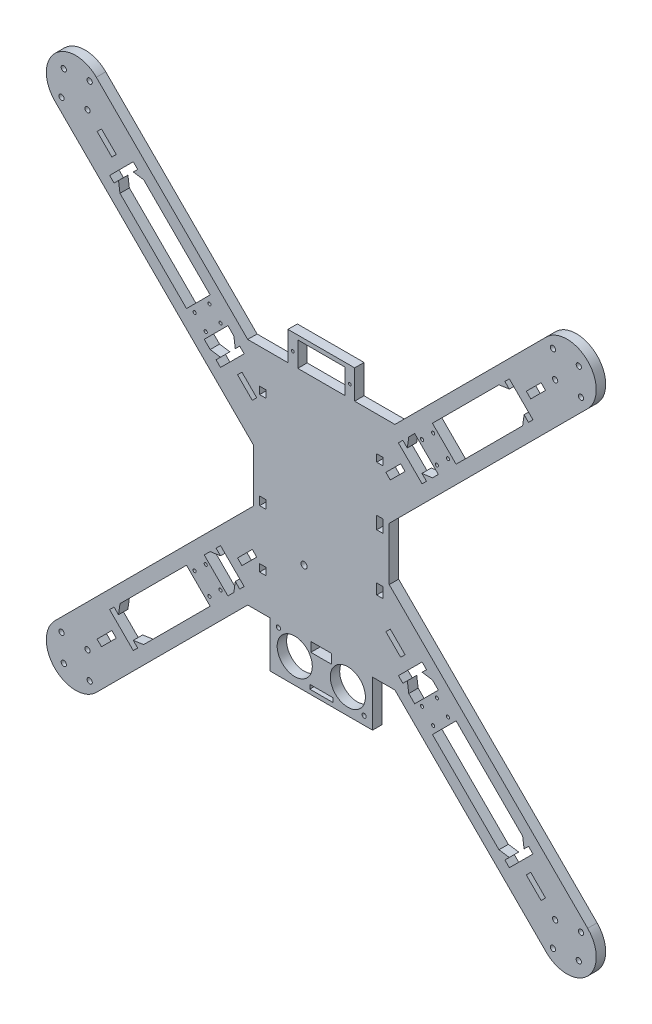
SolidWorks part; units mm, degrees
material "Custom Plastic"
ref_plane "Front Plane" through (0, 0, 0) normal (0, 0, 1) x (1, 0, 0)
ref_plane "Top Plane" through (0, 0, 0) normal (0, 1, 0) x (1, 0, 0)
ref_plane "Right Plane" through (0, 0, 0) normal (1, 0, 0) x (0, 0, -1)
sketch "Sketch1" plane through (0, 0, 0) normal (0, 0, 1) x (1, 0, 0)
  line L0 (117.5, 117.5) -> (-117.5, 117.5) construction
  line L1 (-117.5, 117.5) -> (117.5, -117.5) construction
  line L2 (117.5, -117.5) -> (-117.5, -117.5) construction
  line L3 (-117.5, -117.5) -> (117.5, 117.5) construction
  line L4 (117.5, 117.5) -> (117.5, -117.5) construction
  line L5 (-117.5, 117.5) -> (-117.5, -117.5) construction
  line L6 (0, 117.5) -> (0, -117.5) construction
  line L7 (35.201, 55) -> (15.95, 55)
  line L8 (-32.5, 55) -> (32.5, 55) construction
  line L9 (-35.201, 55) -> (-107.6005, 127.3995)
  line L10 (-127.3995, 107.6005) -> (-32.5, 12.701)
  line L11 (-117.5, 0) -> (117.5, 0) construction
  line L12 (-32.5, 12.701) -> (-32.5, -12.701)
  line L13 (32.5, 55) -> (32.5, -55) construction
  line L14 (32.5, -55) -> (-32.5, -55) construction
  line L15 (-32.5, -55) -> (-32.5, 55) construction
  line L16 (32.5, 55) -> (-32.5, -55) construction
  line L17 (-24.5, -55) -> (-24.5, -77)
  line L18 (-127.3995, -107.6005) -> (-32.5, -12.701)
  line L19 (-24.5, -77) -> (24.5, -77)
  line L20 (-35.201, -55) -> (-107.6005, -127.3995)
  line L21 (35.201, -55) -> (24.5, -55)
  line L22 (35.201, -55) -> (107.6005, -127.3995)
  line L23 (127.3995, -107.6005) -> (32.5, -12.701)
  line L24 (32.5, 12.701) -> (32.5, -12.701)
  line L25 (127.3995, 107.6005) -> (32.5, 12.701)
  line L26 (35.201, 55) -> (107.6005, 127.3995)
  line L27 (24.5, -55) -> (24.5, -77)
  line L28 (-24.5, -55) -> (-35.201, -55)
  line L29 (-15.95, 55) -> (-15.95, 68.8)
  line L30 (-15.95, 68.8) -> (15.95, 68.8)
  line L31 (15.95, 55) -> (15.95, 68.8)
  line L32 (-15.95, 55) -> (-35.201, 55)
  arc A0 (-107.6005, 127.3995) -> (-127.3995, 107.6005) centre (-117.5, 117.5) ccw
  arc A12 (-107.6005, -127.3995) -> (-127.3995, -107.6005) centre (-117.5, -117.5) cw
  arc A16 (107.6005, -127.3995) -> (127.3995, -107.6005) centre (117.5, -117.5) ccw
  arc A24 (107.6005, 127.3995) -> (127.3995, 107.6005) centre (117.5, 117.5) cw
  point P3 (0, 0)
  point P18 (0, 0)
  point P21 (0, -77)
  point P26 (0, 68.8)
  point P33 (-117.5, 117.5)
  point P34 (-32.5, 0)
  point P65 (0, -55)
  point P80 (0, 55)
  dimension "D3" = 14
  dimension "D8" = 24.5
  dimension "D7" = 22
  dimension "D1" = 235
  dimension "D2" = 235
  dimension "D4" = 65
  dimension "D5" = 110
  dimension "D6" = 28
  dimension "D9" = 13.8
  dimension "D10" = 31.9
extrude "Boss-Extrude1" add sketch "Sketch1" against normal blind 4.5
sketch "Sketch4" plane through (0, 0, 0) normal (0, 0, 1) x (1, 0, 0)
  line L0 (0, 0) -> (0, 55) construction
  line L2 (0, 0) -> (-32.5, 0) construction
  line L3 (-32.5, 12.701) -> (-32.5, -12.701) construction
  line L4 (-32.5, 0) -> (-32.5, 12.701) construction
  line L5 (-32.5, 12.701) -> (-127.3995, 107.6005) construction
  line L6 (-35.201, 55) -> (-107.6005, 127.3995) construction
  line L7 (-107.6005, 127.3995) -> (-127.3995, 107.6005) construction
  line L8 (-110.7825, 124.2175) -> (-124.2175, 110.7825) construction
  line L9 (-123.1569, 123.1569) -> (-111.8431, 111.8431) construction
  circle A20 centre (-110.7825, 124.2175) radius 1.25
  circle A21 centre (-124.2175, 110.7825) radius 1.25
  circle A22 centre (-123.1569, 123.1569) radius 1.25
  circle A23 centre (-111.8431, 111.8431) radius 1.25
  circle A24 centre (111.8431, 111.8431) radius 1.25
  circle A25 centre (110.7825, 124.2175) radius 1.25
  circle A26 centre (123.1569, 123.1569) radius 1.25
  circle A27 centre (124.2175, 110.7825) radius 1.25
  circle A28 centre (111.8431, -111.8431) radius 1.25
  circle A29 centre (124.2175, -110.7825) radius 1.25
  circle A30 centre (123.1569, -123.1569) radius 1.25
  circle A31 centre (110.7825, -124.2175) radius 1.25
  circle A32 centre (-111.8431, -111.8431) radius 1.25
  circle A33 centre (-110.7825, -124.2175) radius 1.25
  circle A34 centre (-123.1569, -123.1569) radius 1.25
  circle A35 centre (-124.2175, -110.7825) radius 1.25
  point P16 (-117.5, 117.5)
  point P19 (-117.5, 117.5)
  point P26 (-117.5, 117.5)
  point P62 (0, 0)
  dimension "D1" = 55
  dimension "D4" = 2.5
  dimension "D2" = 19
  dimension "D5" = 35.201
  dimension "D3" = 16
extrude "Cut-Extrude1" cut sketch "Sketch4" against normal blind 4.5
sketch "Sketch5" plane through (0, 0, 0) normal (0, 0, 1) x (1, 0, 0)
  line L4 (0, 0) -> (0, 14.0392) construction
  line L6 (15.95, 68.8) -> (-15.95, 68.8) construction
  line L7 (-11.25, 66.8) -> (-11.25, 55)
  line L8 (-11.25, 55) -> (11.25, 55)
  line L9 (11.25, 55) -> (11.25, 66.8)
  line L10 (11.25, 66.8) -> (-11.25, 66.8)
  line L12 (0, 66.8) -> (0, 55) construction
  line L13 (-13.65, 60.9) -> (13.65, 60.9) construction
  circle A2 centre (-13.65, 60.9) radius 0.65
  circle A3 centre (13.65, 60.9) radius 0.65
  point P20 (0, 60.9)
  point P21 (0, 60.9)
  dimension "D8" = 1.3
  dimension "D9" = 1.3
  dimension "D2" = 2
  dimension "D10" = 27.3
  dimension "D11" = 22.5
  dimension "D12" = 11.8
extrude "Cut-Extrude2" cut sketch "Sketch5" against normal blind 4.5
sketch "Sketch6" plane through (0, 0, 0) normal (0, 0, 1) x (1, 0, 0)
  line L1 (-11.25, 55) -> (11.25, 55) construction
  circle A0 centre (-8.25, -25) radius 1.5
  dimension "D3" = 3
  dimension "D1" = 80
  dimension "D2" = 3
extrude "Cut-Extrude3" cut sketch "Sketch6" against normal blind 4.5
sketch "Sketch7" plane through (0, 0, 0) normal (0, 0, 1) x (1, 0, 0)
  line L0 (-22.5, -55) -> (-22.5, -75) construction
  line L5 (-22.5, -75) -> (22.5, -75) construction
  line L6 (22.5, -75) -> (22.5, -55) construction
  line L7 (22.5, -55) -> (-22.5, -55) construction
  line L8 (0, -55) -> (0, -75) construction
  line L9 (-12.7, -65) -> (0, -65) construction
  line L10 (-24.5, -77) -> (24.5, -77) construction
  line L11 (-24.5, -55) -> (-24.5, -77) construction
  line L12 (-5, -55) -> (-5, -59.5)
  line L13 (-5, -59.5) -> (5, -59.5)
  line L15 (5, -55) -> (-5, -55)
  line L16 (-5.5, -75) -> (-5.5, -73)
  line L17 (-5.5, -73) -> (5.5, -73)
  line L21 (5.5, -75) -> (-5.5, -75)
  line L22 (5, -55) -> (5, -59.5)
  line L23 (5.5, -75) -> (5.5, -73)
  circle A5 centre (-20.5, -57) radius 1
  circle A6 centre (-12.7, -65) radius 8.4
  circle A7 centre (12.7, -65) radius 8.4
  circle A8 centre (20.5, -73) radius 1
  point P25 (0, -59.5)
  point P26 (0, -73)
  dimension "D3" = 2
  dimension "D6" = 20
  dimension "D13" = 5.5
  dimension "D5" = 45
  dimension "D1" = 2
  dimension "D4" = 16.8
  dimension "D14" = 2
  dimension "D2" = 2
  dimension "D7" = 2
  dimension "D8" = 2
  dimension "D9" = 12.7
  dimension "D10" = 5
  dimension "D11" = 4.5
  dimension "D12" = 2
  dimension "D15" = 2
  dimension "D16" = 2
extrude "Cut-Extrude4" cut sketch "Sketch7" against normal blind 4.5
sketch "Sketch8" plane through (0, 0, 0) normal (0, 0, 1) x (1, 0, 0)
  line L0 (101.2365, -89.9228) -> (89.9228, -101.2365)
  line L1 (89.9228, -101.2365) -> (87.8015, -99.1152)
  line L2 (36.8898, -48.2035) -> (48.2035, -36.8898)
  line L3 (48.2035, -36.8898) -> (50.3249, -39.0111)
  line L4 (105.4792, -85.6802) -> (85.6802, -105.4792) construction
  line L5 (127.3995, -107.6005) -> (32.5, -12.701) construction
  line L6 (35.201, -55) -> (107.6005, -127.3995) construction
  line L7 (40.0718, -37.9505) -> (37.9505, -40.0718)
  line L8 (115.8431, -107.8431) -> (111.8431, -111.8431) construction
  line L9 (37.9505, -40.0718) -> (30.8794, -33.0007)
  line L10 (50.3249, 39.0111) -> (48.2035, 36.8898)
  line L11 (30.8794, -33.0007) -> (33.0007, -30.8794)
  line L12 (33.0007, -30.8794) -> (40.0718, -37.9505)
  line L13 (42.5467, -42.5467) -> (39.0111, -39.0111) construction
  line L14 (35.201, -55) -> (107.6005, -127.3995) construction
  line L15 (100.1759, -98.0546) -> (98.0546, -100.1759)
  line L16 (98.0546, -100.1759) -> (105.1256, -107.247)
  line L17 (105.1256, -107.247) -> (107.247, -105.1256)
  line L18 (107.247, -105.1256) -> (100.1759, -98.0546)
  line L19 (99.1152, -99.1152) -> (95.5797, -95.5797) construction
  line L20 (-101.2365, -89.9228) -> (-99.1152, -87.8015)
  line L21 (-100.1759, -98.0546) -> (-107.247, -105.1256)
  line L22 (-107.247, -105.1256) -> (-105.1256, -107.247)
  line L23 (-105.1256, -107.247) -> (-98.0546, -100.1759)
  line L24 (-98.0546, -100.1759) -> (-100.1759, -98.0546)
  line L25 (-89.9228, -101.2365) -> (-101.2365, -89.9228)
  line L26 (-36.8898, -48.2035) -> (-39.0111, -50.3249)
  line L27 (-48.2035, -36.8898) -> (-36.8898, -48.2035)
  line L28 (-37.9505, -40.0718) -> (-40.0718, -37.9505)
  line L29 (-30.8794, -33.0007) -> (-37.9505, -40.0718)
  line L30 (-40.0718, -37.9505) -> (-33.0007, -30.8794)
  line L31 (-33.0007, -30.8794) -> (-30.8794, -33.0007)
  line L32 (-89.9228, 101.2365) -> (-87.8015, 99.1152)
  line L33 (-98.0546, 100.1759) -> (-105.1256, 107.247)
  line L34 (-105.1256, 107.247) -> (-107.247, 105.1256)
  line L35 (-107.247, 105.1256) -> (-100.1759, 98.0546)
  line L36 (-100.1759, 98.0546) -> (-98.0546, 100.1759)
  line L37 (-101.2365, 89.9228) -> (-89.9228, 101.2365)
  line L38 (-48.2035, 36.8898) -> (-50.3249, 39.0111)
  line L39 (-36.8898, 48.2035) -> (-48.2035, 36.8898)
  line L40 (-40.0718, 37.9505) -> (-37.9505, 40.0718)
  line L41 (-33.0007, 30.8794) -> (-40.0718, 37.9505)
  line L42 (-37.9505, 40.0718) -> (-30.8794, 33.0007)
  line L43 (-30.8794, 33.0007) -> (-33.0007, 30.8794)
  line L44 (101.2365, 89.9228) -> (99.1152, 87.8015)
  line L45 (100.1759, 98.0546) -> (107.247, 105.1256)
  line L46 (107.247, 105.1256) -> (105.1256, 107.247)
  line L47 (105.1256, 107.247) -> (98.0546, 100.1759)
  line L48 (98.0546, 100.1759) -> (100.1759, 98.0546)
  line L49 (89.9228, 101.2365) -> (101.2365, 89.9228)
  line L50 (36.8898, 48.2035) -> (39.0111, 50.3249)
  line L51 (48.2035, 36.8898) -> (36.8898, 48.2035)
  line L52 (37.9505, 40.0718) -> (40.0718, 37.9505)
  line L53 (30.8794, 33.0007) -> (37.9505, 40.0718)
  line L54 (40.0718, 37.9505) -> (33.0007, 30.8794)
  line L55 (33.0007, 30.8794) -> (30.8794, 33.0007)
  line L56 (32.5, 12.701) -> (127.3995, 107.6005) construction
  line L57 (41.8396, 53.1533) -> (84.9731, 96.2868)
  line L58 (96.2868, 84.9731) -> (53.1533, 41.8396)
  line L59 (87.8015, 99.1152) -> (89.9228, 101.2365)
  line L60 (99.1152, -87.8015) -> (96.9939, -89.9228)
  line L61 (-96.2868, -84.9731) -> (-53.1533, -41.8396)
  line L62 (96.9939, -89.9228) -> (96.2868, -84.9731)
  line L63 (99.1152, -87.8015) -> (101.2365, -89.9228)
  line L64 (87.8015, -99.1152) -> (89.9228, -96.9939)
  line L65 (-87.8015, -99.1152) -> (-89.9228, -101.2365)
  line L66 (89.9228, -96.9939) -> (84.9731, -96.2868)
  line L67 (84.9731, -96.2868) -> (41.8396, -53.1533)
  line L68 (50.3249, -39.0111) -> (48.2035, -41.1325)
  line L69 (48.2035, -41.1325) -> (53.1533, -41.8396)
  line L70 (53.1533, -41.8396) -> (96.2868, -84.9731)
  line L71 (39.0111, -50.3249) -> (41.1325, -48.2035)
  line L72 (41.1325, -48.2035) -> (41.8396, -53.1533)
  line L73 (39.0111, -50.3249) -> (36.8898, -48.2035)
  line L74 (-89.9228, -96.9939) -> (-84.9731, -96.2868)
  line L75 (-87.8015, -99.1152) -> (-89.9228, -96.9939)
  line L76 (-96.9939, -89.9228) -> (-96.2868, -84.9731)
  line L77 (-99.1152, -87.8015) -> (-96.9939, -89.9228)
  line L78 (-41.1325, -48.2035) -> (-41.8396, -53.1533)
  line L79 (-39.0111, -50.3249) -> (-41.1325, -48.2035)
  line L80 (-48.2035, -41.1325) -> (-53.1533, -41.8396)
  line L81 (-50.3249, -39.0111) -> (-48.2035, -41.1325)
  line L82 (-96.9939, 89.9228) -> (-96.2868, 84.9731)
  line L83 (-99.1152, 87.8015) -> (-96.9939, 89.9228)
  line L84 (-89.9228, 96.9939) -> (-84.9731, 96.2868)
  line L85 (-87.8015, 99.1152) -> (-89.9228, 96.9939)
  line L86 (-48.2035, 41.1325) -> (-53.1533, 41.8396)
  line L87 (-50.3249, 39.0111) -> (-48.2035, 41.1325)
  line L88 (-41.1325, 48.2035) -> (-41.8396, 53.1533)
  line L89 (-39.0111, 50.3249) -> (-41.1325, 48.2035)
  line L90 (89.9228, 96.9939) -> (84.9731, 96.2868)
  line L91 (87.8015, 99.1152) -> (89.9228, 96.9939)
  line L92 (96.9939, 89.9228) -> (96.2868, 84.9731)
  line L93 (99.1152, 87.8015) -> (96.9939, 89.9228)
  line L94 (41.1325, 48.2035) -> (41.8396, 53.1533)
  line L95 (39.0111, 50.3249) -> (41.1325, 48.2035)
  line L96 (48.1429, 41.1931) -> (53.1533, 41.8396)
  line L97 (50.3249, 39.0111) -> (48.1429, 41.1931)
  line L98 (-39.0111, 50.3249) -> (-36.8898, 48.2035)
  line L99 (-53.1533, 41.8396) -> (-96.2868, 84.9731)
  line L100 (-99.1152, 87.8015) -> (-101.2365, 89.9228)
  line L101 (-84.9731, 96.2868) -> (-41.8396, 53.1533)
  line L102 (-41.8396, -53.1533) -> (-84.9731, -96.2868)
  line L103 (-50.3249, -39.0111) -> (-48.2035, -36.8898)
  line L104 (96.2868, 84.9731) -> (84.9731, 96.2868) construction
  line L105 (53.1533, 41.8396) -> (41.8396, 53.1533) construction
  point P10 (95.5797, -95.5797)
  point P11 (95.5797, -95.5797)
  point P18 (-49.2642, 40.0718)
  point P19 (-49.2642, -40.0718)
  point P68 (0, 0)
  point P122 (0, 0)
  dimension "D1" = 23
  dimension "D2" = 75
  dimension "D3" = 3
  dimension "D4" = 10
  dimension "D5" = 5
  dimension "D6" = 6
  dimension "D7" = 3
  dimension "D8" = 10
  dimension "D9" = 5
  dimension "D11" = 6
  dimension "D12" = 3
  dimension "D13" = 4
  dimension "D14" = 3
  dimension "D15" = 3
  dimension "D16" = 4
  dimension "D17" = 3
  dimension "D18" = 3
  dimension "D19" = 4
  dimension "D20" = 3
  dimension "D21" = 3
  dimension "D22" = 4
  dimension "D23" = 3
  dimension "D24" = 3
  dimension "D25" = 4
  dimension "D26" = 3
  dimension "D27" = 4
  dimension "D28" = 3
  dimension "D29" = 3
  dimension "D30" = 4
  dimension "D31" = 4
  dimension "D32" = 3
  dimension "D33" = 3
  dimension "D34" = 4
  dimension "D35" = 4
  dimension "D36" = 3
  dimension "D37" = 3
  dimension "D38" = 4
  dimension "D39" = 4
  dimension "D40" = 3
  dimension "D41" = 3
  dimension "D42" = 4
  dimension "D43" = 4
  dimension "D10" = 4
extrude "Cut-Extrude5" cut sketch "Sketch8" against normal through all
sketch "Sketch9" plane through (-5.6569, 5.6569, 0) normal (0.7071, -0.7071, 0) x (0, 0, -1)
  line L0 (4.5, 128.1701) -> (4.5, 67.1701) construction
  line L1 (4.5, 83.1701) -> (0, 83.1701)
  line L2 (4.5, 83.1701) -> (4.5, 71.1701)
  line L3 (4.5, 71.1701) -> (0, 71.1701)
  line L4 (0, 83.1701) -> (0, 71.1701)
  line L5 (0, 128.1701) -> (0, 67.1701) construction
  line L6 (0, 0) -> (28.0274, 0) construction
  line L7 (4.5, 63.1701) -> (0, 63.1701) construction
  dimension "D1" = 8
  dimension "D2" = 12
extrude "Boss-Extrude2" add sketch "Sketch9" along normal up to next
sketch "Sketch11" plane through (5.6569, 5.6569, 0) normal (-0.7071, -0.7071, 0) x (0, 0, 1)
  line L0 (-4.5, -128.1701) -> (-4.5, -67.1701) construction
  line L1 (-4.5, -71.1701) -> (0, -71.1701)
  line L2 (-4.5, -71.1701) -> (-4.5, -83.1701)
  line L3 (-4.5, -83.1701) -> (0, -83.1701)
  line L4 (0, -71.1701) -> (0, -83.1701)
  line L5 (0, -128.1701) -> (0, -67.1701) construction
  line L6 (-4.5, -63.1701) -> (0, -63.1701) construction
  dimension "D1" = 8
  dimension "D2" = 12
extrude "Boss-Extrude3" add sketch "Sketch11" along normal up to next
sketch "Sketch12" plane through (5.6569, -5.6569, 0) normal (-0.7071, 0.7071, 0) x (0, 0, 1)
  line L0 (-4.5, -128.1701) -> (-4.5, -67.1701) construction
  line L1 (-4.5, -71.1701) -> (0, -71.1701)
  line L2 (-4.5, -71.1701) -> (-4.5, -83.1701)
  line L3 (-4.5, -83.1701) -> (0, -83.1701)
  line L4 (0, -71.1701) -> (0, -83.1701)
  line L5 (0, -128.1701) -> (0, -67.1701) construction
  dimension "D1" = 8
  dimension "D2" = 12
extrude "Boss-Extrude4" add sketch "Sketch12" along normal up to next
sketch "Sketch13" plane through (5.6569, 5.6569, 0) normal (-0.7071, -0.7071, 0) x (0, 0, 1)
  line L0 (-4.5, 67.1701) -> (-4.5, 128.1701) construction
  line L1 (-4.5, 71.1701) -> (0, 71.1701)
  line L2 (-4.5, 71.1701) -> (-4.5, 83.1701)
  line L3 (-4.5, 83.1701) -> (0, 83.1701)
  line L4 (0, 71.1701) -> (0, 83.1701)
  line L5 (0, 67.1701) -> (0, 128.1701) construction
  dimension "D1" = 8
  dimension "D2" = 12
extrude "Boss-Extrude5" add sketch "Sketch13" along normal up to next
sketch "Sketch14" plane through (0, 0, -4.5) normal (0, 0, -1) x (-1, 0, 0)
  line L0 (32.5, 0) -> (-32.5, 0) construction
  line L1 (32.5, 12.701) -> (32.5, -12.701) construction
  line L2 (-32.5, -12.701) -> (-32.5, 12.701) construction
  line L3 (28, -38.5) -> (28, 38.5) construction
  line L14 (-26.5, 13) -> (-26.5, 7)
  line L17 (-26.5, 7) -> (-29.5, 7)
  line L19 (-26.5, 13) -> (-29.5, 13)
  line L23 (26.5, -38.5) -> (29.5, -38.5)
  line L24 (26.5, -38.5) -> (26.5, -35)
  line L25 (26.5, -35) -> (29.5, -35)
  line L26 (29.5, -38.5) -> (29.5, -35)
  line L27 (26.5, -11) -> (29.5, -11)
  line L28 (26.5, -11) -> (26.5, -7)
  line L29 (26.5, -7) -> (29.5, -7)
  line L30 (29.5, -11) -> (29.5, -7)
  line L31 (26.5, 35) -> (29.5, 35)
  line L32 (26.5, 35) -> (26.5, 38.5)
  line L33 (26.5, 38.5) -> (29.5, 38.5)
  line L34 (29.5, 35) -> (29.5, 38.5)
  line L35 (-29.5, 13) -> (-29.5, 7)
  line L36 (32.5, 12.701) -> (32.5, -12.701) construction
  line L37 (-26.5, -20) -> (-29.5, -20)
  line L38 (-26.5, -20) -> (-26.5, -15)
  line L39 (-26.5, -15) -> (-29.5, -15)
  line L40 (-29.5, -20) -> (-29.5, -15)
  line L41 (-26.5, 35) -> (-29.5, 35)
  line L42 (-26.5, 35) -> (-26.5, 38.5)
  line L43 (-26.5, 38.5) -> (-29.5, 38.5)
  line L44 (-29.5, 35) -> (-29.5, 38.5)
  line L45 (-32.5, -12.701) -> (-32.5, 12.701) construction
  point P11 (28, -38.5)
  point P16 (28, 0)
  point P28 (-28, 13)
  point P38 (-28, 7)
  dimension "D2" = 3
  dimension "D3" = 3.5
  dimension "D4" = 24
  dimension "D5" = 7
  dimension "D6" = 22
  dimension "D7" = 6
  dimension "D8" = 3.5
  dimension "D9" = 22
  dimension "D10" = 4
  dimension "D11" = 3.5
  dimension "D12" = 42
  dimension "D13" = 5
  dimension "D14" = 3
  dimension "D15" = 3
  dimension "D16" = 3
  dimension "D17" = 7
extrude "Cut-Extrude6" cut sketch "Sketch14" against normal through all
sketch "Sketch15" plane through (0, 0, -4.5) normal (0, 0, -1) x (-1, 0, 0)
  line L0 (-55.2746, -48.2035) -> (-48.2035, -55.2746) construction
  line L1 (-48.2035, -55.2746) -> (-53.5068, -60.5779) construction
  line L2 (-53.5068, -60.5779) -> (-60.5779, -53.5068) construction
  line L3 (-60.5779, -53.5068) -> (-55.2746, -48.2035) construction
  line L4 (-64.2902, -44.4912) -> (-44.4912, -64.2902) construction
  line L5 (-127.3995, -107.6005) -> (-32.5, -12.701) construction
  line L6 (-35.201, -55) -> (-107.6005, -127.3995) construction
  line L7 (-57.0424, -57.0424) -> (-51.7391, -51.7391) construction
  line L8 (-53.1533, -64.467) -> (-64.467, -53.1533) construction
  circle A6 centre (-60.5779, -53.5068) radius 0.75
  circle A7 centre (-55.2746, -48.2035) radius 0.75
  circle A8 centre (-48.2035, -55.2746) radius 0.75
  circle A9 centre (-53.5068, -60.5779) radius 0.75
  circle A10 centre (-53.5068, 60.5779) radius 0.75
  circle A11 centre (-48.2035, 55.2746) radius 0.75
  circle A12 centre (-60.5779, 53.5068) radius 0.75
  circle A13 centre (-55.2746, 48.2035) radius 0.75
  circle A14 centre (60.5779, 53.5068) radius 0.75
  circle A15 centre (55.2746, 48.2035) radius 0.75
  circle A16 centre (53.5068, 60.5779) radius 0.75
  circle A17 centre (48.2035, 55.2746) radius 0.75
  circle A18 centre (53.5068, -60.5779) radius 0.75
  circle A19 centre (48.2035, -55.2746) radius 0.75
  circle A20 centre (60.5779, -53.5068) radius 0.75
  circle A21 centre (55.2746, -48.2035) radius 0.75
  point P12 (-54.3907, -54.3907)
  point P19 (-54.3907, -54.3907)
  point P47 (0, 0)
  dimension "D3" = 1.5
  dimension "D1" = 7.5
  dimension "D2" = 10
  dimension "D4" = 2.5
  dimension "D5" = 4
extrude "Cut-Extrude7" cut sketch "Sketch15" against normal through all
